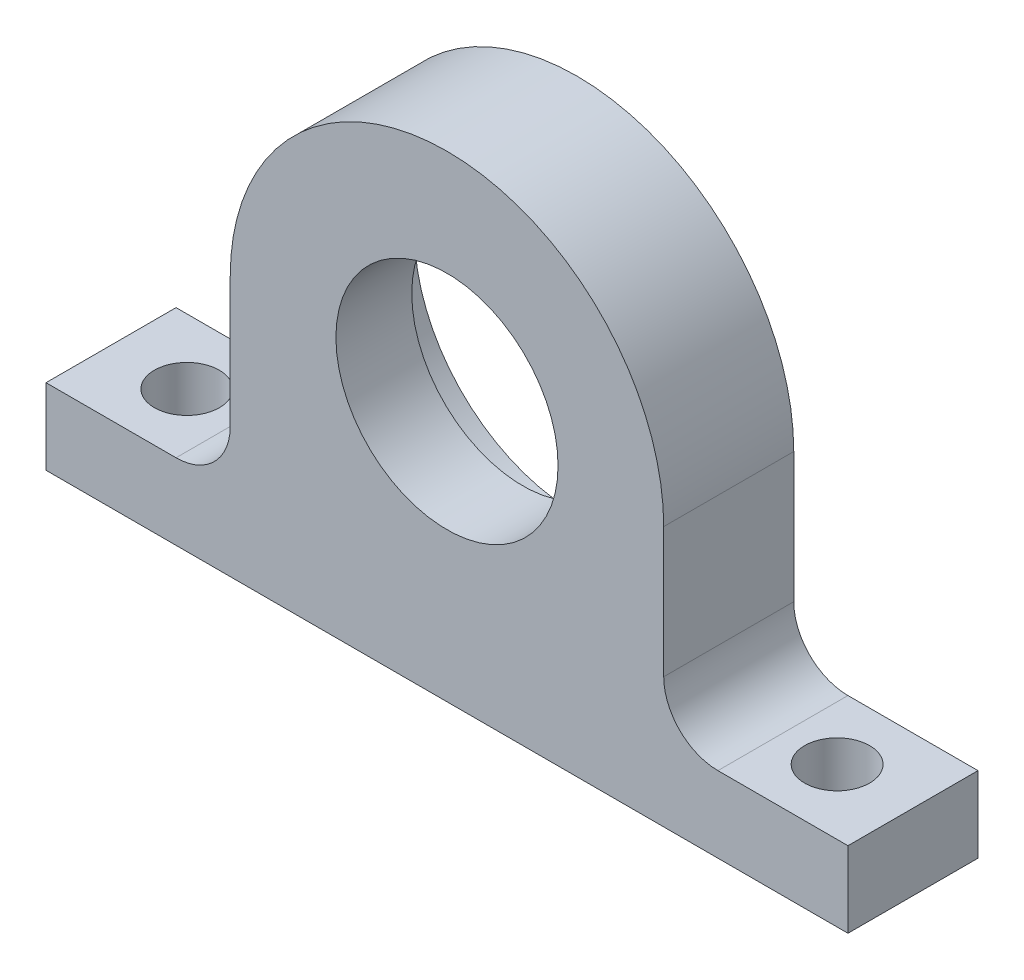
SolidWorks part; units mm, degrees
material "6061-T6 (SS)"
ref_plane "Front Plane" through (0, 0, 0) normal (0, 0, 1) x (1, 0, 0)
ref_plane "Top Plane" through (0, 0, 0) normal (0, 1, 0) x (1, 0, 0)
ref_plane "Right Plane" through (0, 0, 0) normal (1, 0, 0) x (0, 0, -1)
sketch "Sketch1" plane through (0, 0, 0) normal (0, 0, 1) x (1, 0, 0)
  line L0 (-10.5357, -17) -> (-37, -17)
  line L1 (-37, -17) -> (-37, -24)
  line L2 (-37, -24) -> (0, -24)
  line L3 (0, 0) -> (0, 38.453) construction
  line L4 (37, -24) -> (0, -24)
  line L5 (37, -17) -> (37, -24)
  line L6 (10.5357, -17) -> (37, -17)
  circle A0 centre (0, 0) radius 10.25
  arc A2 (10.5357, -17) -> (-10.5357, -17) centre (0, 0) ccw
  point P16 (-10.5357, -17)
  point P19 (10.5357, -17)
  dimension "D1" = 20.5
  dimension "D2" = 74
  dimension "D3" = 17
  dimension "D5" = 20
  dimension "D4" = 7
extrude "Boss-Extrude1" add sketch "Sketch1" along normal blind 12
sketch "Sketch2" plane through (0, -17, 0) normal (0, 1, 0) x (1, 0, 0)
  line L0 (37, -12) -> (37, 0) construction
  line L2 (0, 0) -> (0, 23.6093) construction
  circle A0 centre (30, -6) radius 3
  circle A1 centre (-30, -6) radius 3
  point P5 (37, -6)
  dimension "D1" = 6
  dimension "D2" = 7
extrude "Cut-Extrude1" cut sketch "Sketch2" against normal through all
sketch "Sketch3" plane through (0, 0, 0) normal (0, 0, -1) x (-1, 0, 0)
  circle A0 centre (0, 0) radius 15
  dimension "D1" = 30
extrude "Cut-Extrude2" cut sketch "Sketch3" against normal blind 5
sketch "Sketch4" plane through (0, 0, 0) normal (0, 0, -1) x (-1, 0, 0)
  line L1 (-20, 0) -> (-10.5357, -17)
  line L2 (-10.5357, -17) -> (-20, -17)
  line L3 (0, 0) -> (0, -6.2592) construction
  line L4 (20, 0) -> (20, -17)
  line L5 (10.5357, -17) -> (20, -17)
  line L6 (-20, 0) -> (-20, -17)
  line L7 (20, 0) -> (10.5357, -17)
  arc A1 (10.5357, -17) -> (-10.5357, -17) centre (0, 0) ccw construction
extrude "Boss-Extrude2" add sketch "Sketch4" against normal through all
fillet "Fillet2" radius 5 2 edges at (-20, -17, 6) (20, -17, 6)
